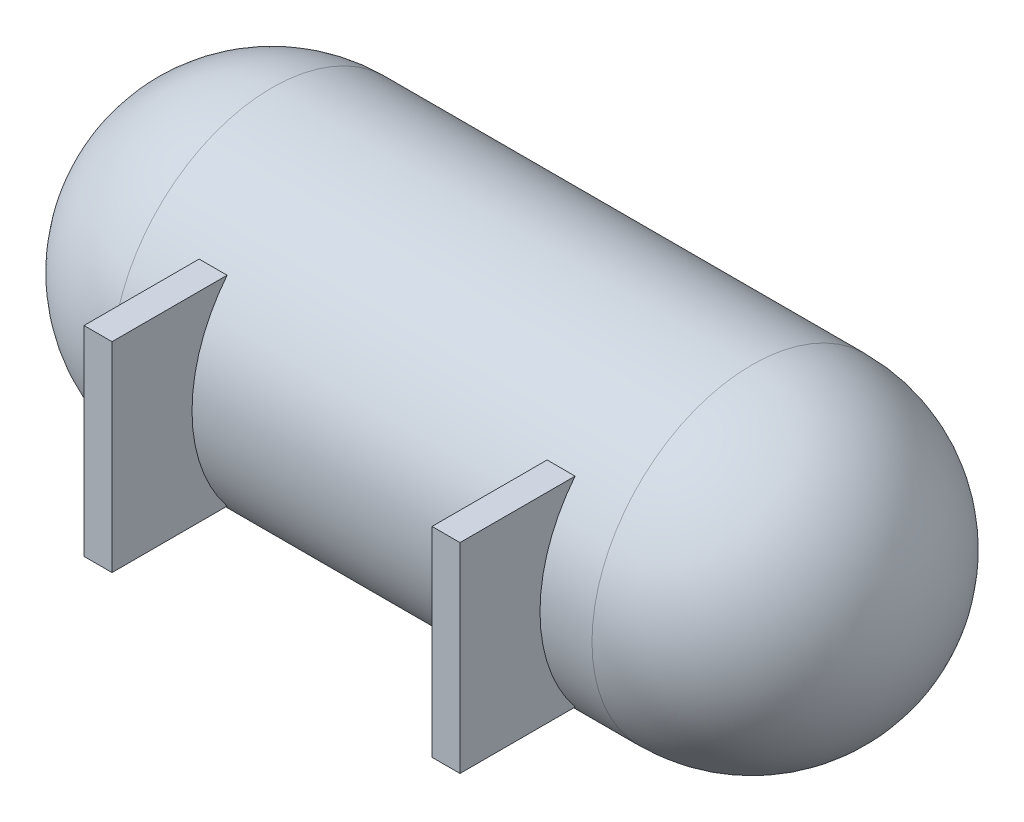
SolidWorks part; units mm, degrees
material "11 500"
ref_plane "Přední rovina" through (0, 0, 0) normal (0, 0, 1) x (1, 0, 0)
ref_plane "Vrchní rovina" through (0, 0, 0) normal (0, 1, 0) x (1, 0, 0)
ref_plane "Pravá rovina" through (0, 0, 0) normal (1, 0, 0) x (0, 0, -1)
sketch "Skica1" plane through (0, 0, 0) normal (0, 0, 1) x (1, 0, 0)
  line L0 (200, 200) -> (800, 200)
  line L1 (200, 190) -> (800, 190)
  line L2 (1000, 0) -> (990, 0)
  line L3 (0, 0) -> (10, 0)
  line L4 (0, 0) -> (50000, 0) construction
  arc A0 (800, 200) -> (1000, 0) centre (800, 0) cw
  arc A1 (200, 200) -> (0, 0) centre (200, 0) ccw
  arc A2 (800, 190) -> (990, 0) centre (800, 0) cw
  arc A3 (200, 190) -> (10, 0) centre (200, 0) ccw
  dimension "D1" = 200
  dimension "D2" = 1000
  dimension "D3" = 10
revolve "Rotovat1" add sketch "Skica1" angle 360 about L4
ref_plane "Rovina1" through (0, 0, 300) normal (0, 0, 1) x (1, 0, 0)
sketch "Skica2" plane through (0, 0, 300) normal (0, 0, 1) x (1, 0, 0)
  line L0 (735, -125) -> (735, 125)
  line L1 (735, 125) -> (700, 125)
  line L2 (700, 125) -> (700, -125)
  line L3 (700, -125) -> (735, -125)
  line L4 (500, -107.13) -> (500, 353.2776) construction
  line L5 (800, 200) -> (800, -200) construction
  line L6 (200, 200) -> (200, -200) construction
  line L7 (0, 0) -> (765.0542, 0) construction
  line L8 (265, 125) -> (300, 125)
  line L9 (265, -125) -> (265, 125)
  line L10 (300, -125) -> (265, -125)
  line L11 (300, 125) -> (300, -125)
  dimension "D1" = 250
  dimension "D2" = 35
  dimension "D3" = 200
extrude "Přidat vysunutím2" add sketch "Skica2" against normal up to surface (143.8751 mm away)
